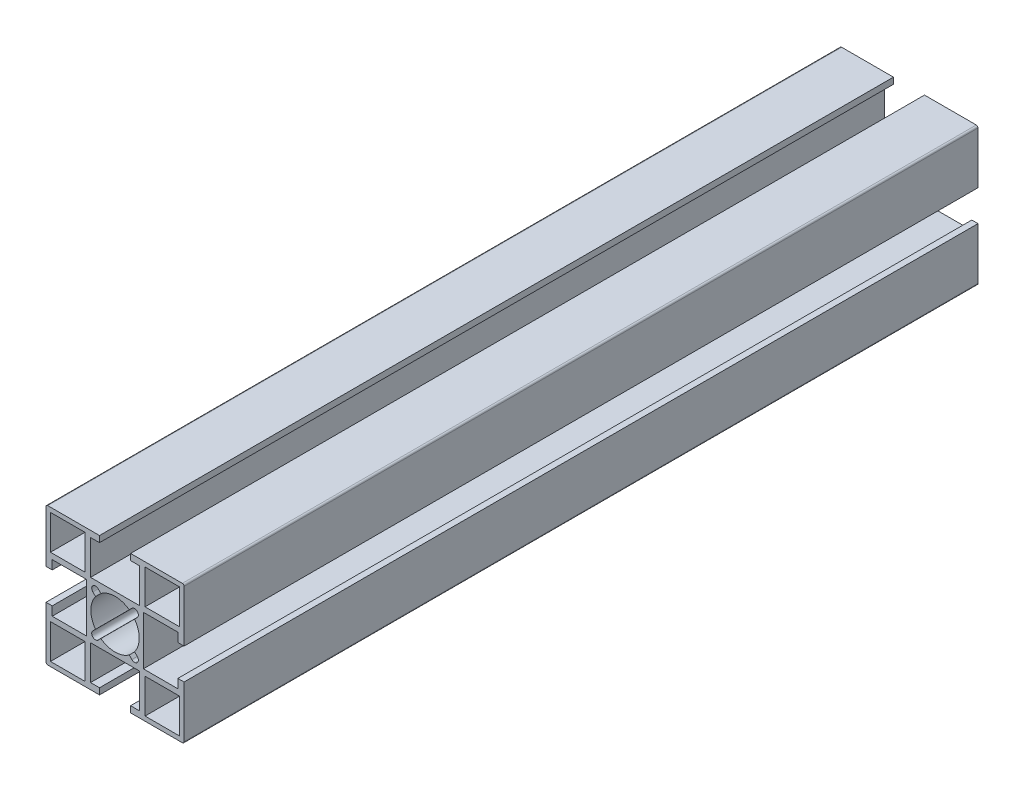
SolidWorks part; units mm, degrees
ref_plane "前视基准面" through (0, 0, 0) normal (0, 0, 1) x (1, 0, 0)
ref_plane "上视基准面" through (0, 0, 0) normal (0, 1, 0) x (1, 0, 0)
ref_plane "右视基准面" through (0, 0, 0) normal (1, 0, 0) x (0, 0, -1)
other "Configuration Table"
sketch "草图1" plane through (0, 0, 0) normal (1, 0, 0) x (0, 0, -1)
  line L0 (0, 0) -> (230, 0)
  dimension "D1" = 230
other "铝型材 40 X 40A X R0.5(1)"
ref_plane "基准面1" through (0, 0, 0) normal (0, 0, -1) x (0, 1, 0)
sketch "Sketch1" plane through (0, 0, 0) normal (0, 0, -1) x (0, 1, 0)
  line L0 (0, 0) -> (0, 16.3773) construction
  line L1 (0, 0) -> (-5.6569, 5.6569) construction
  line L2 (-19.5, 20) -> (-4.5, 20)
  line L3 (-20, 19.5) -> (-20, 4.5)
  line L4 (-19.5, -20) -> (-4.5, -20)
  line L5 (20, 19.5) -> (20, 4.5)
  line L6 (-4.879, 6.4347) -> (-4.1104, 5.6661)
  line L7 (-6.4347, 4.879) -> (-5.6661, 4.1104)
  line L8 (6.4347, 4.879) -> (5.6661, 4.1104)
  line L9 (0, 0) -> (20, 0) construction
  line L10 (4.879, 6.4347) -> (4.1104, 5.6661)
  line L11 (4.879, -6.4347) -> (4.1104, -5.6661)
  line L12 (6.4347, -4.879) -> (5.6661, -4.1104)
  line L13 (-6.4347, -4.879) -> (-5.6661, -4.1104)
  line L14 (-4.879, -6.4347) -> (-4.1104, -5.6661)
  line L15 (-4.5, 20) -> (-4.5, 18.2)
  line L16 (-18.7, 18.7) -> (-8.7, 18.7)
  line L17 (-18.7, 18.7) -> (-18.7, 8.7)
  line L18 (-18.7, 8.7) -> (-8.7, 8.7)
  line L19 (-8.7, 18.7) -> (-8.7, 8.7)
  line L20 (-7.1, 18.2) -> (-4.5, 18.2)
  line L21 (-7.1, 18.2) -> (-7.1, 8.2)
  line L22 (-7.1, 8.2) -> (7.1, 8.2)
  line L23 (7.1, 18.2) -> (7.1, 8.2)
  line L24 (4.5, 20) -> (4.5, 18.2)
  line L25 (4.5, 20) -> (19.5, 20)
  line L26 (4.5, 18.2) -> (7.1, 18.2)
  line L27 (8.7, 18.7) -> (8.7, 8.7)
  line L28 (18.7, 8.7) -> (8.7, 8.7)
  line L29 (18.7, 18.7) -> (18.7, 8.7)
  line L30 (18.7, 18.7) -> (8.7, 18.7)
  line L31 (18.2, 7.1) -> (8.2, 7.1)
  line L32 (18.2, 7.1) -> (18.2, 4.5)
  line L33 (20, 4.5) -> (18.2, 4.5)
  line L34 (8.2, 7.1) -> (8.2, -7.1)
  line L35 (18.2, -7.1) -> (8.2, -7.1)
  line L36 (18.2, -4.5) -> (18.2, -7.1)
  line L37 (20, -4.5) -> (18.2, -4.5)
  line L38 (7.1, -18.2) -> (7.1, -8.2)
  line L39 (7.1, -18.2) -> (4.5, -18.2)
  line L40 (4.5, -20) -> (4.5, -18.2)
  line L41 (7.1, -8.2) -> (-7.1, -8.2)
  line L42 (-7.1, -18.2) -> (-7.1, -8.2)
  line L43 (-4.5, -18.2) -> (-7.1, -18.2)
  line L44 (-4.5, -20) -> (-4.5, -18.2)
  line L45 (-18.2, -7.1) -> (-8.2, -7.1)
  line L46 (-18.2, -7.1) -> (-18.2, -4.5)
  line L47 (-20, -4.5) -> (-18.2, -4.5)
  line L48 (-8.2, -7.1) -> (-8.2, 7.1)
  line L49 (-18.2, 7.1) -> (-8.2, 7.1)
  line L50 (-18.2, 4.5) -> (-18.2, 7.1)
  line L51 (-20, 4.5) -> (-18.2, 4.5)
  line L52 (4.5, -20) -> (19.5, -20)
  line L53 (-20, -4.5) -> (-20, -19.5)
  line L54 (20, -4.5) -> (20, -19.5)
  line L55 (18.7, -18.7) -> (18.7, -8.7)
  line L56 (18.7, -8.7) -> (8.7, -8.7)
  line L57 (8.7, -18.7) -> (8.7, -8.7)
  line L58 (18.7, -18.7) -> (8.7, -18.7)
  line L59 (-8.7, -18.7) -> (-8.7, -8.7)
  line L60 (-18.7, -8.7) -> (-8.7, -8.7)
  line L61 (-18.7, -18.7) -> (-8.7, -18.7)
  line L62 (-18.7, -18.7) -> (-18.7, -8.7)
  arc A0 (-4.1104, 5.6661) -> (4.1104, 5.6661) centre (0, 0) cw
  arc A1 (-4.879, 6.4347) -> (-6.4347, 4.879) centre (-5.6569, 5.6569) ccw
  arc A2 (-4.1104, -5.6661) -> (4.1104, -5.6661) centre (0, 0) ccw
  arc A3 (-5.6661, 4.1104) -> (-5.6661, -4.1104) centre (0, 0) ccw
  arc A4 (6.4347, 4.879) -> (4.879, 6.4347) centre (5.6569, 5.6569) ccw
  arc A5 (4.879, -6.4347) -> (6.4347, -4.879) centre (5.6569, -5.6569) ccw
  arc A6 (-6.4347, -4.879) -> (-4.879, -6.4347) centre (-5.6569, -5.6569) ccw
  arc A7 (5.6661, 4.1104) -> (5.6661, -4.1104) centre (0, 0) cw
  arc A8 (-19.5, 20) -> (-20, 19.5) centre (-19.5, 19.5) ccw
  arc A9 (19.5, 20) -> (20, 19.5) centre (19.5, 19.5) cw
  arc A10 (19.5, -20) -> (20, -19.5) centre (19.5, -19.5) ccw
  arc A11 (-20, -19.5) -> (-19.5, -20) centre (-19.5, -19.5) ccw
  point P86 (20, 20)
  point P87 (-20, 20)
  point P88 (-20, -20)
  point P89 (20, -20)
  point P90 (0, 0)
  dimension "D2" = 7
  dimension "D3" = 45
  dimension "D4" = 1.1
  dimension "D5" = 1.8
  dimension "D6" = 8
  dimension "D7" = 1.3
  dimension "D8" = 14.2
  dimension "D10" = 10
  dimension "D11" = 10
  dimension "D12" = 40
  dimension "D13" = 9
  dimension "D14" = 0.5
  dimension "D9" = 1.3
